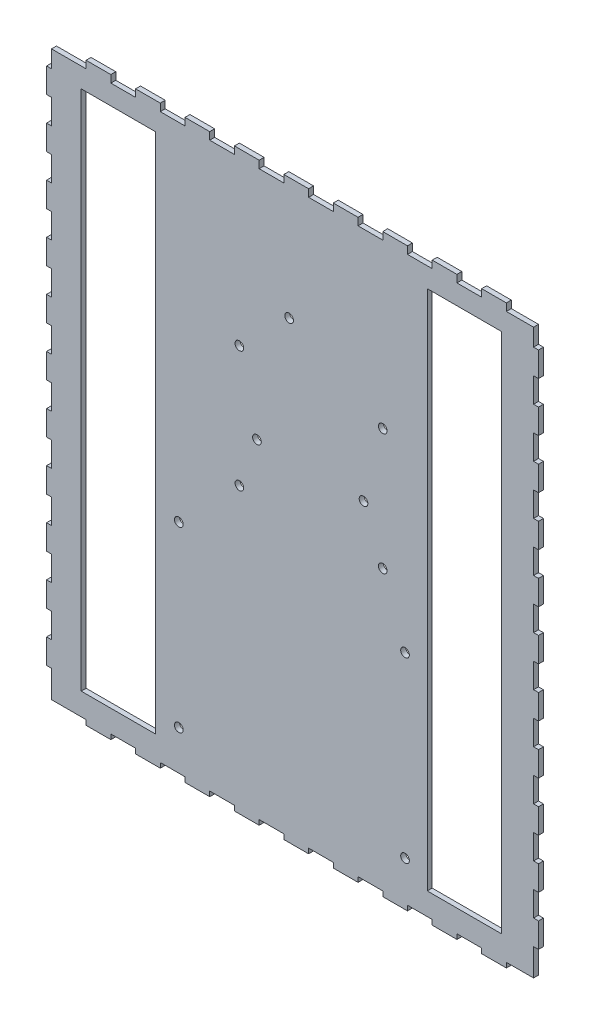
SolidWorks part; units mm, degrees
material "Verre"
ref_plane "Front Plane" through (0, 0, 0) normal (0, 0, 1) x (1, 0, 0)
ref_plane "Top Plane" through (0, 0, 0) normal (0, 1, 0) x (1, 0, 0)
ref_plane "Right Plane" through (0, 0, 0) normal (1, 0, 0) x (0, 0, -1)
sketch "Sketch1" plane through (0, 0, 0) normal (0, 0, 1) x (1, 0, 0)
  line L1 (0, 0) -> (194, 0)
  line L2 (0, 0) -> (0, 227)
  line L3 (0, 227) -> (194, 227)
  line L4 (194, 0) -> (194, 227)
  dimension "D1" = 194
  dimension "D2" = 227
extrude "Boss-Extrude1" add sketch "Sketch1" along normal blind 2
sketch "Sketch2" plane through (194, 0, 0) normal (1, 0, 0) x (0, 0, -1)
  line L0 (-2, 0) -> (-2, 227) construction
  line L1 (-2, 10) -> (0, 10)
  line L2 (-2, 10) -> (-2, 20)
  line L3 (-2, 20) -> (0, 20)
  line L4 (0, 10) -> (0, 20)
  line L5 (0, 0) -> (0, 227) construction
  line L6 (-2, 0) -> (0, 0) construction
  dimension "D1" = 10
  dimension "D2" = 10
extrude "Boss-Extrude2" add sketch "Sketch2" along normal blind 3
pattern_linear "LPattern1" count 11 spacing 20 along (0, 1, 0) of "Boss-Extrude2"
sketch "Sketch4" plane through (0, 0, 0) normal (-1, 0, 0) x (0, 0, 1)
  line L0 (0, 227) -> (0, 0) construction
  line L1 (0, 10) -> (2, 10)
  line L2 (0, 10) -> (0, 20)
  line L3 (0, 20) -> (2, 20)
  line L4 (2, 10) -> (2, 20)
  line L5 (2, 227) -> (2, 0) construction
  line L6 (2, 0) -> (0, 0) construction
  dimension "D1" = 10
  dimension "D2" = 10
extrude "Boss-Extrude3" add sketch "Sketch4" along normal blind 3
pattern_linear "LPattern2" count 11 spacing 20 along (0, 1, 0) of "Boss-Extrude3"
sketch "Sketch5" plane through (0, 0, 0) normal (0, -1, 0) x (1, 0, 0)
  line L0 (0, 0) -> (194, 0) construction
  line L1 (184, 0) -> (174, 0)
  line L2 (184, 0) -> (184, 2)
  line L3 (184, 2) -> (174, 2)
  line L4 (174, 0) -> (174, 2)
  line L5 (0, 2) -> (194, 2) construction
  line L6 (194, 2) -> (194, 0) construction
  point P10 (194, 1)
  dimension "D1" = 10
  dimension "D2" = 10
extrude "Boss-Extrude4" add sketch "Sketch5" along normal blind 3
pattern_linear "LPattern3" count 9 spacing 20 along (-1, 0, 0) of "Boss-Extrude4"
sketch "Sketch6" plane through (0, 227, 0) normal (0, 1, 0) x (1, 0, 0)
  line L0 (194, -2) -> (0, -2) construction
  line L1 (184, -2) -> (174, -2)
  line L2 (184, -2) -> (184, 0)
  line L3 (184, 0) -> (174, 0)
  line L4 (174, -2) -> (174, 0)
  line L5 (194, 0) -> (0, 0) construction
  line L6 (194, -2) -> (194, 0) construction
  dimension "D1" = 10
  dimension "D2" = 10
extrude "Boss-Extrude5" add sketch "Sketch6" along normal blind 3
pattern_linear "LPattern4" count 9 spacing 20 along (-1, 0, 0) of "Boss-Extrude5"
sketch "Sketch7" plane through (0, 0, 2) normal (0, 0, 1) x (1, 0, 0)
  line L0 (0, 170) -> (0, 160) construction
  line L5 (12, 8) -> (42, 8)
  line L6 (12, 8) -> (12, 219)
  line L7 (12, 219) -> (42, 219)
  line L8 (42, 8) -> (42, 219)
  line L9 (34, 227) -> (24, 227) construction
  line L10 (24, 0) -> (34, 0) construction
  dimension "D1" = 12
  dimension "D2" = 8
  dimension "D3" = 8
  dimension "D4" = 30
extrude "Cut-Extrude1" cut sketch "Sketch7" against normal through all
sketch "Sketch8" plane through (0, 0, 2) normal (0, 0, 1) x (1, 0, 0)
  line L0 (194, 0) -> (194, 10) construction
  line L1 (42, 219) -> (12, 219) construction
  line L2 (182, 8) -> (152, 8)
  line L3 (182, 8) -> (182, 219)
  line L4 (182, 219) -> (152, 219)
  line L5 (152, 8) -> (152, 219)
  line L6 (12, 8) -> (42, 8) construction
  line L7 (194, 140) -> (194, 150) construction
  line L8 (194, 100) -> (194, 110) construction
  line L9 (44, 0) -> (54, 0) construction
  circle A0 centre (143, 15) radius 1.75
  circle A1 centre (51.5, 15) radius 1.75
  circle A2 centre (143, 87) radius 1.75
  circle A3 centre (51.5, 87) radius 1.75
  circle A4 centre (134, 112) radius 1.75
  circle A5 centre (76, 112) radius 1.75
  circle A6 centre (134, 161) radius 1.75
  circle A7 centre (76, 161) radius 1.75
  dimension "D1" = 3.5
  dimension "D7" = 3.5
  dimension "D2" = 91.5
  dimension "D3" = 72
  dimension "D4" = 51
  dimension "D5" = 12
  dimension "D6" = 30
  dimension "D8" = 49
  dimension "D9" = 58
  dimension "D10" = 60
  dimension "D11" = 25
  dimension "D12" = 15
extrude "Cut-Extrude2" cut sketch "Sketch8" against normal through all
sketch "Esquisse1" plane through (0, 0, 0) normal (0, 0, -1) x (-1, 0, 0)
  line L0 (3, 220) -> (0, 220) construction
  line L1 (3, 220) -> (2, 220)
  line L2 (3, 220) -> (3, -11.6309)
  line L3 (3, -11.6309) -> (2, -11.6309)
  line L4 (2, 220) -> (2, -11.6309)
  line L5 (3, 220) -> (3, 210) construction
  dimension "D1" = 1
extrude "Enlèv. mat.-Extru.1" cut sketch "Esquisse1" against normal up to next
sketch "Esquisse2" plane through (0, 0, 0) normal (0, 0, -1) x (-1, 0, 0)
  line L1 (-194, 227) -> (-195, 227)
  line L2 (-194, 227) -> (-194, 0)
  line L3 (-194, 0) -> (-195, 0)
  line L4 (-195, 227) -> (-195, 0)
  line L5 (-195, 0) -> (0, 0)
  line L6 (-195, 0) -> (-195, -1)
  line L7 (-195, -1) -> (0, -1)
  line L8 (0, 0) -> (0, -1)
  dimension "D1" = 1
  dimension "D2" = 1
extrude "Boss.-Extru.1" add sketch "Esquisse2" against normal blind 2 contours L8 L5 L3 L6 L7
sketch "Esquisse3" plane through (0, 0, 0) normal (0, 0, -1) x (-1, 0, 0)
  circle A0 centre (-96.1127, 180.7744) radius 1.75
  circle A1 centre (-126.2127, 131.6744) radius 1.75
  circle A2 centre (-83.1127, 131.6744) radius 1.75
  dimension "D1" = 3.5
  dimension "D2" = 3.5
  dimension "D3" = 3.5
extrude "Enlèv. mat.-Extru.2" cut sketch "Esquisse3" against normal through all
